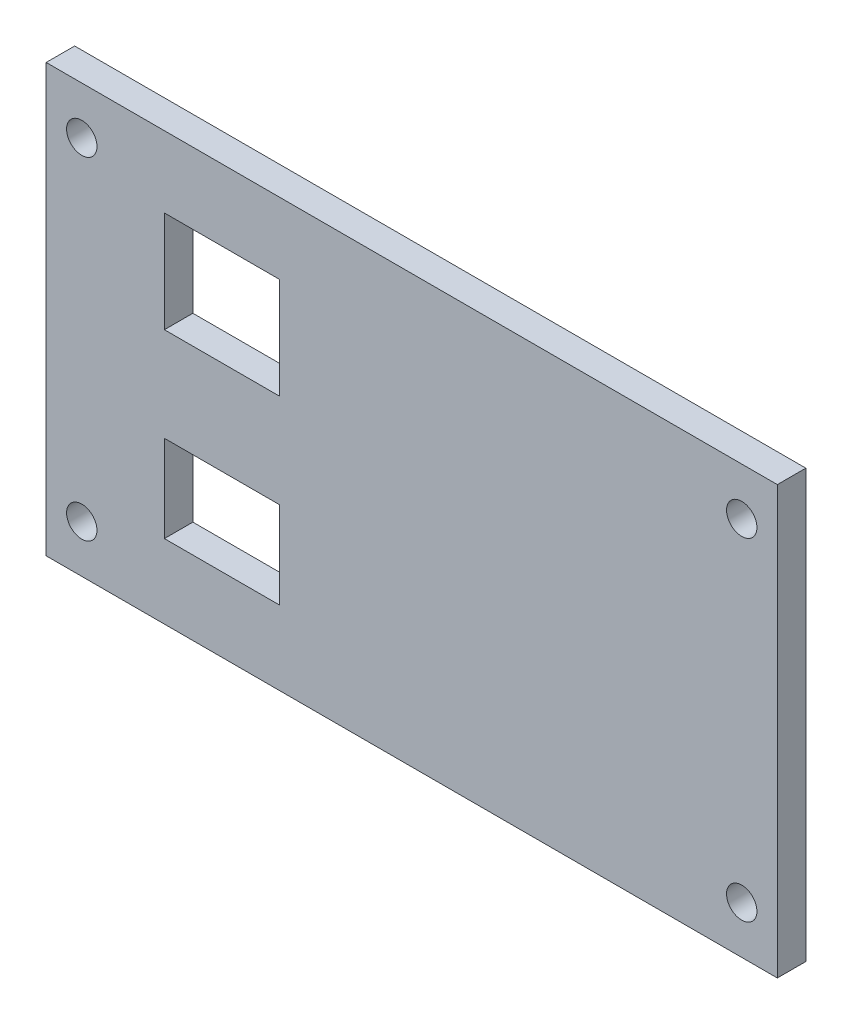
SolidWorks part; units mm, degrees
ref_plane "Alzado" through (0, 0, 0) normal (0, 0, 1) x (1, 0, 0)
ref_plane "Planta" through (0, 0, 0) normal (0, 1, 0) x (1, 0, 0)
ref_plane "Vista lateral" through (0, 0, 0) normal (1, 0, 0) x (0, 0, -1)
sketch "Croquis1" plane through (0, 0, 0) normal (0, 0, 1) x (1, 0, 0)
  line L1 (38.5, -22.5) -> (-38.5, -22.5)
  line L2 (38.5, -22.5) -> (38.5, 22.5)
  line L3 (38.5, 22.5) -> (-38.5, 22.5)
  line L4 (-38.5, -22.5) -> (-38.5, 22.5)
  line L5 (38.5, -22.5) -> (-38.5, 22.5) construction
  line L6 (38.5, 22.5) -> (-38.5, -22.5) construction
  point P0 (0, 0)
  dimension "D1" = 77
  dimension "D2" = 45
extrude "Saliente-Extruir1" add sketch "Croquis1" along normal blind 3
sketch "Croquis2" plane through (0, 0, 0) normal (0, 0, -1) x (-1, 0, 0)
  line L0 (-38.5, 22.5) -> (38.5, 22.5) construction
  line L1 (26.05, 15) -> (13.95, 15)
  line L2 (26.05, 15) -> (26.05, 4.35)
  line L3 (26.05, 4.35) -> (13.95, 4.35)
  line L4 (13.95, 15) -> (13.95, 4.35)
  line L5 (26.05, -5.55) -> (13.95, -5.55)
  line L6 (26.05, -5.55) -> (26.05, -14.7)
  line L7 (26.05, -14.7) -> (13.95, -14.7)
  line L8 (13.95, -5.55) -> (13.95, -14.7)
  line L9 (38.5, 22.5) -> (38.5, -22.5) construction
  line L10 (34.75, -17.5) -> (38.5, -17.5) construction
  line L11 (34.75, 17.5) -> (-34.75, 17.5) construction
  line L12 (34.75, 17.5) -> (34.75, -17.5) construction
  line L13 (34.75, -17.5) -> (-34.75, -17.5) construction
  line L14 (-34.75, 17.5) -> (-34.75, -17.5) construction
  line L15 (34.75, -22.5) -> (34.75, -17.5) construction
  line L16 (38.5, -22.5) -> (-38.5, -22.5) construction
  line L17 (38.5, 22.5) -> (38.5, -22.5) construction
  line L18 (-34.75, 17.5) -> (-34.75, 22.5) construction
  line L19 (-38.5, 22.5) -> (38.5, 22.5) construction
  line L20 (-34.75, 17.5) -> (-38.5, 17.5) construction
  line L21 (-38.5, -22.5) -> (-38.5, 22.5) construction
  circle A0 centre (34.75, 17.5) radius 1.6
  circle A1 centre (-34.75, 17.5) radius 1.6
  circle A2 centre (-34.75, -17.5) radius 1.6
  circle A3 centre (34.75, -17.5) radius 1.6
  dimension "D9" = 3.2
  dimension "D1" = 7.5
  dimension "D2" = 18.15
  dimension "D3" = 28.05
  dimension "D4" = 37.2
  dimension "D5" = 12.45
  dimension "D6" = 24.55
  dimension "D7" = 69.5
  dimension "D8" = 35
extrude "Cortar-Extruir1" cut sketch "Croquis2" against normal up to next
